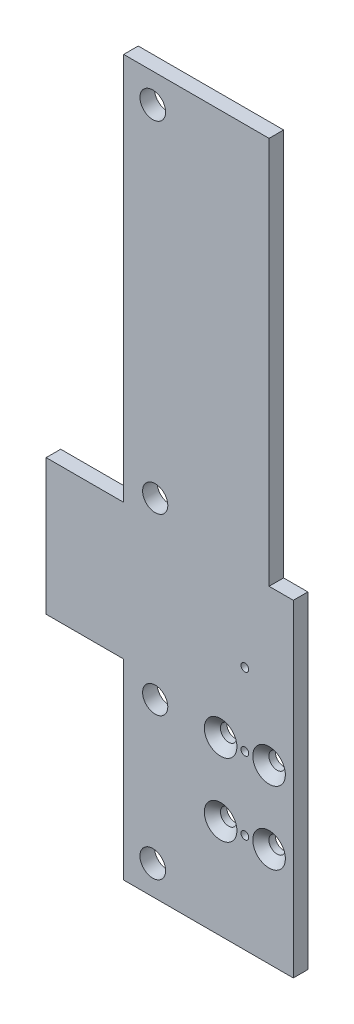
SolidWorks part; units mm, degrees
material "6061 Alloy"
ref_plane "Front Plane" through (0, 0, 0) normal (0, 0, 1) x (1, 0, 0)
ref_plane "Top Plane" through (0, 0, 0) normal (0, 1, 0) x (1, 0, 0)
ref_plane "Right Plane" through (0, 0, 0) normal (1, 0, 0) x (0, 0, -1)
sketch "Sketch1" plane through (0, 0, 0) normal (0, 0, 1) x (1, 0, 0)
  line L1 (-10, -20) -> (10, -20)
  line L2 (-10, -20) -> (-10, 20)
  line L3 (-10, 20) -> (10, 20)
  line L4 (10, -20) -> (10, 20)
  line L5 (-10, -20) -> (10, 20) construction
  line L6 (-10, 20) -> (10, -20) construction
  point P0 (0, 0)
  dimension "D1" = 20
  dimension "D2" = 40
extrude "Boss-Extrude1" add sketch "Sketch1" along normal blind 3
hole_wizard "CSK for M3 Hex Socket Countersunk Cap Screw1" positions "Sketch2" profile "Sketch3" countersink size "M3" standard "ISO" end condition through all
sketch "Sketch2" plane through (0, 0, 3) normal (0, 0, 1) x (1, 0, 0)
  line L0 (5, -15) -> (5, 0) construction
  line L1 (5, 0) -> (-5, 0) construction
  line L2 (-5, 0) -> (-5, -15) construction
  line L3 (-5, -15) -> (5, -15) construction
  line L7 (10, 20) -> (-10, 20) construction
  line L8 (0.0001, -15) -> (0, -20) construction
  line L9 (-10, -20) -> (10, -20) construction
  line L12 (-10, 20) -> (-10, -20) construction
  point P0 (-5, 0)
  point P2 (5, 0)
  point P4 (5, -15)
  point P6 (-5, -15)
  dimension "D1" = 10
  dimension "D2" = 15
  dimension "D3" = 20
  dimension "D4" = 5
sketch "Sketch3" plane through (-5, 0, 3) normal (1, 0, 0) x (0, -1, 0)
  line L0 (0, 0) -> (0, 3)
  line L1 (0, 3) -> (1.7, 3)
  line L2 (1.7, 3) -> (1.7, 1.66)
  line L3 (1.7, 1.66) -> (3.36, 0)
  line L5 (3.36, 0) -> (0, 0)
  line L6 (-1.7, 1.66) -> (-3.36, 0) construction
  line L11 (0, -6.35) -> (0, 107.95) construction
  dimension "Thru Hole Dia." = 3.4
  dimension "Thru Hole Depth" = 3
  dimension "Near C'Sink Dia." = 6.72
  dimension "Near C'Sink Angle" = 90
hole_wizard "M2 Tapped Hole1" positions "Sketch4" profile "Sketch5" tap size "M2" standard "ISO" end condition through all
sketch "Sketch4" plane through (0, 0, 3) normal (0, 0, 1) x (1, 0, 0)
  line L0 (0, 0) -> (0, 15) construction
  line L2 (0, -15) -> (0, 0) construction
  line L4 (10, 20) -> (-10, 20) construction
  point P0 (0, 15)
  point P2 (0, 0)
  point P4 (0, -15)
  dimension "D1" = 15
  dimension "D2" = 5
  dimension "D3" = 15
sketch "Sketch5" plane through (0, 15, 3) normal (1, 0, 0) x (0, -1, 0)
  line L0 (0, 0) -> (0, 3)
  line L1 (0, 3) -> (0.8, 3)
  line L2 (0.8, 3) -> (0.8, 0)
  line L5 (0.8, 0) -> (0, 0)
  line L11 (0, -6.35) -> (0, 107.95) construction
  dimension "Thru Tap Drill Dia." = 1.6
  dimension "Thru Tap Drill Depth" = 3
cosmetic thread "Hole Thread1" parameters "D2"=2
cosmetic thread "Hole Thread2" parameters "D2"=2
cosmetic thread "Hole Thread3" parameters "D2"=2
sketch "Sketch6" plane through (0, 0, 3) normal (0, 0, 1) x (1, 0, 0)
  line L0 (-10, 4) -> (-41, 4)
  line L2 (-41, 4) -> (-41, 32)
  line L3 (-41, 32) -> (10, 32)
  line L7 (-10, 20) -> (-10, -20) construction
  line L8 (-10, 4) -> (-10, 20)
  line L9 (-10, 20) -> (10, 20)
  line L10 (10, 20) -> (10, 32)
  circle A0 centre (-5, 0) radius 3.36 construction
  dimension "D1" = 31
  dimension "D2" = 28
  dimension "D3" = 4
extrude "Boss-Extrude2" add sketch "Sketch6" against normal blind 3
sketch "Sketch7" plane through (0, 0, 3) normal (0, 0, 1) x (1, 0, 0)
  line L0 (-25, 32) -> (-25, 112.0532)
  line L1 (10, 32) -> (-41, 32) construction
  line L2 (-25, 112.0532) -> (5, 112.0532)
  line L3 (5, 112.0532) -> (5, 32)
  line L4 (5, 32) -> (-25, 32)
  line L5 (10, -20) -> (10, 32) construction
  line L6 (3.2, 96.5532) -> (-3.2, 96.5532) construction
  circle A0 centre (-19, 106.0532) radius 2.65
  dimension "D4" = 5.3
  dimension "D1" = 5
  dimension "D2" = 24
  dimension "D3" = 9.5
  dimension "D5" = 6
  dimension "D6" = 6
extrude "Boss-Extrude3" add sketch "Sketch7" against normal blind 3
sketch "Sketch8" plane through (0, 0, 3) normal (0, 0, 1) x (1, 0, 0)
  line L0 (-10, -20) -> (10, -20) construction
  line L1 (5, 32) -> (5, 112.0532) construction
  line L2 (-25, 4) -> (-25, -35.5)
  line L3 (-41, 4) -> (-10, 4) construction
  line L4 (-25, -35.5) -> (10, -35.5)
  line L5 (10, -35.5) -> (10, -20)
  line L6 (10, -20) -> (-10, -20)
  line L7 (-10, -20) -> (-10, 4)
  line L8 (-10, 4) -> (-25, 4)
  circle A0 centre (-19, -29.5) radius 2.65
  circle A1 centre (-19, 106.0532) radius 2.65 construction
  dimension "D1" = 9.5
  dimension "D2" = 24
  dimension "D3" = 6
  dimension "D4" = 6
extrude "Boss-Extrude4" add sketch "Sketch8" against normal blind 3
sketch "Sketch9" plane through (0, 0, 3) normal (0, 0, 1) x (1, 0, 0)
  line L0 (-41, 4) -> (-25, 4) construction
  line L1 (-25, 4) -> (-25, -35.5) construction
  line L2 (-41, 18) -> (-8.8737, 18) construction
  line L3 (-41, 32) -> (-41, 4) construction
  circle A0 centre (-18.5, 0) radius 2.6
  circle A1 centre (-18.5, 36) radius 2.6
  dimension "D1" = 5.2
  dimension "D2" = 4
  dimension "D3" = 6.5
extrude "Cut-Extrude1" cut sketch "Sketch9" against normal through all
